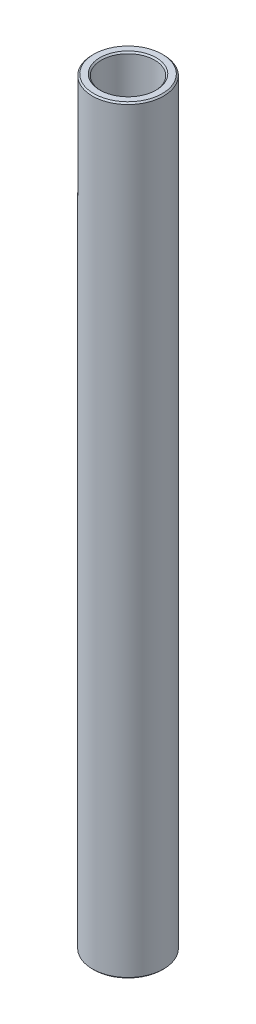
SolidWorks part; units mm, degrees
ref_plane "Front Plane" through (0, 0, 0) normal (0, 0, 1) x (1, 0, 0)
ref_plane "Top Plane" through (0, 0, 0) normal (0, 1, 0) x (1, 0, 0)
ref_plane "Right Plane" through (0, 0, 0) normal (1, 0, 0) x (0, 0, -1)
sketch "Sketch1" plane through (0, 0, 0) normal (0, 0, 1) x (1, 0, 0)
  line L0 (4.7625, 70.6437) -> (4.7625, 205.9781)
  line L1 (4.7625, 205.9781) -> (6.35, 205.9781)
  line L2 (6.35, 205.9781) -> (6.35, 70.6437)
  line L3 (6.35, 70.6437) -> (4.7625, 70.6437)
  line L4 (-10.0875, 90.9128) -> (-120.0875, 90.9128) construction
  line L6 (0, 61.1187) -> (0, 215.5031) construction
  dimension "D1" = 9.525
  dimension "D2" = 9.525
  dimension "D3" = 12.7
  dimension "D4" = 9.525
revolve "Revolve1" add sketch "Sketch1" angle 360 about L6
chamfer "Chamfer1" distance 0.254 angle 45 4 edges at (6.35, 205.9781, 0) (4.7625, 205.9781, 0) (4.7625, 70.6437, 0) (6.35, 70.6437, 0)
equation "\"D4@Sketch1\"=\"D1@Sketch1\""
